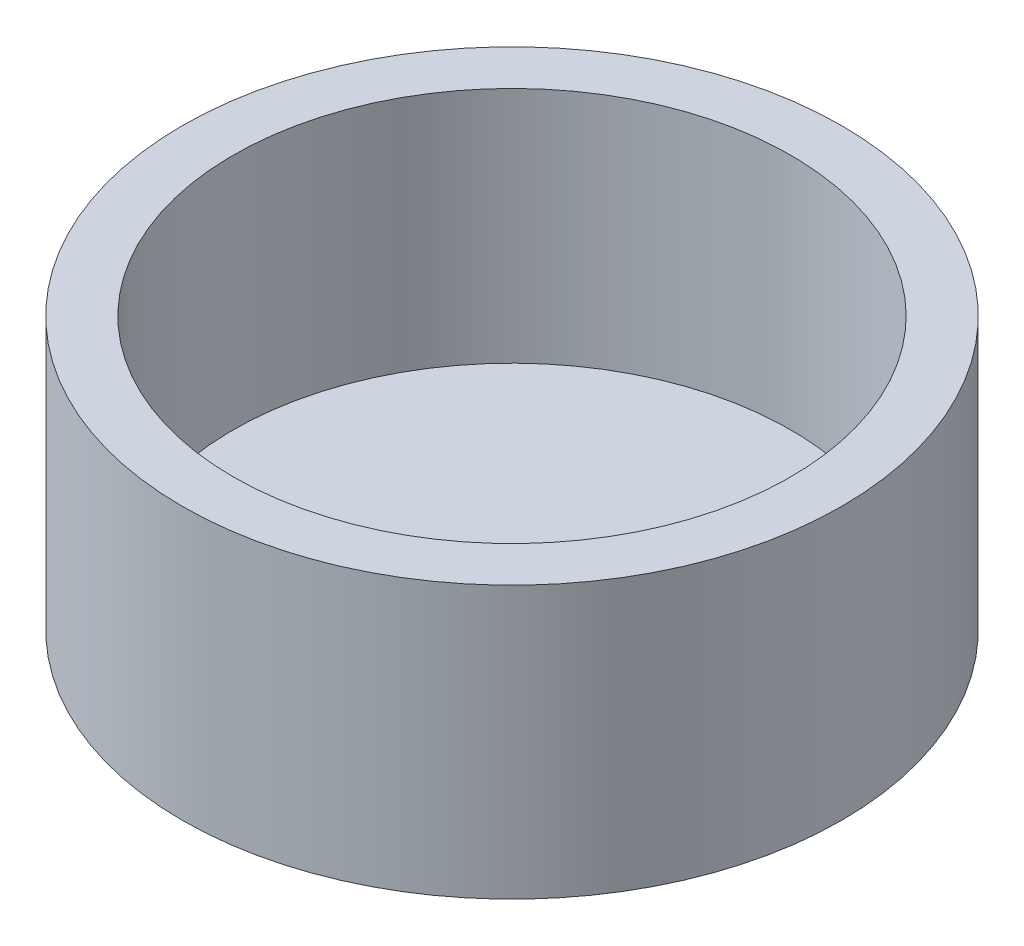
SolidWorks part; units mm, degrees
ref_plane "Front Plane" through (0, 0, 0) normal (0, 0, 1) x (1, 0, 0)
ref_plane "Top Plane" through (0, 0, 0) normal (0, 1, 0) x (1, 0, 0)
ref_plane "Right Plane" through (0, 0, 0) normal (1, 0, 0) x (0, 0, -1)
sketch "Sketch1" plane through (0, 0, 0) normal (0, 1, 0) x (1, 0, 0)
  circle A0 centre (0, 0) radius 4.85
extrude "Boss-Extrude1" add sketch "Sketch1" along normal blind 4
sketch "Sketch2" plane through (0, 4, 0) normal (0, 1, 0) x (1, 0, 0)
  circle A0 centre (0, 0) radius 4.1
extrude "Cut-Extrude1" cut sketch "Sketch2" against normal blind 3.5
